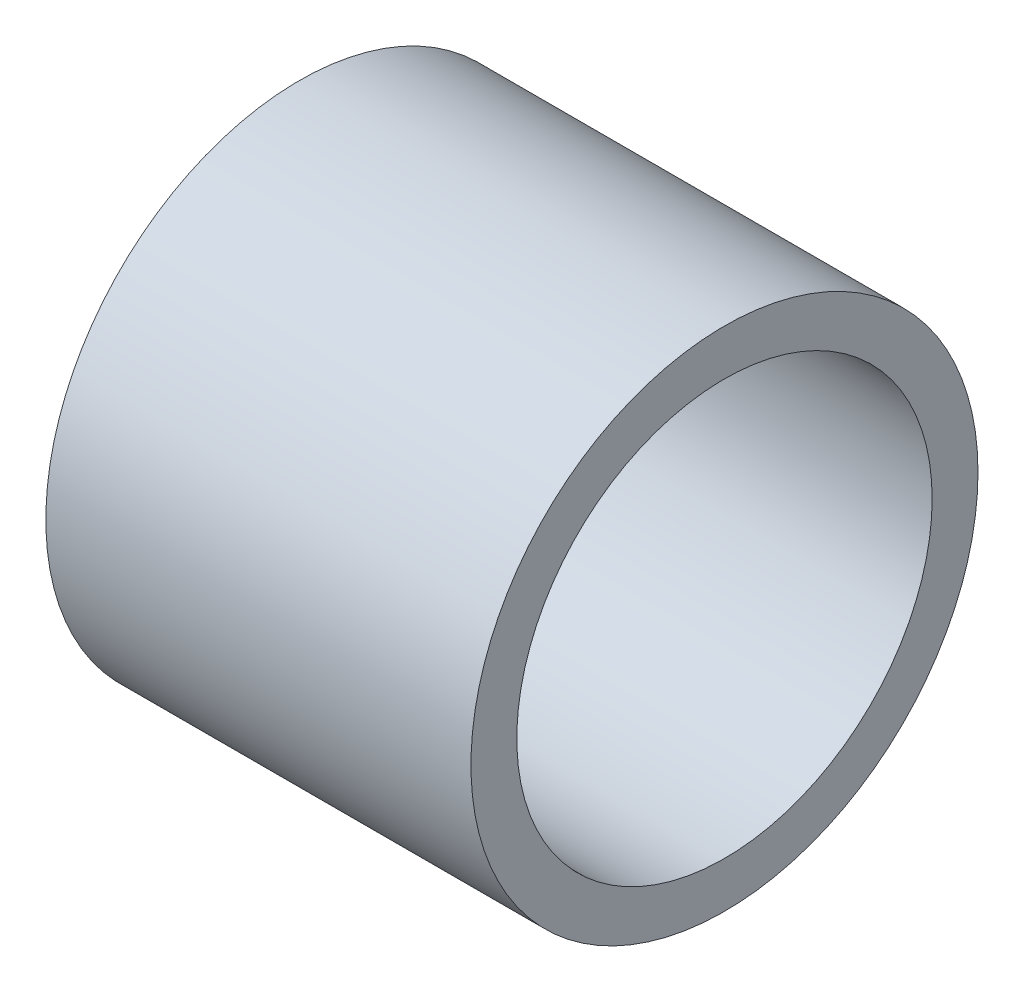
SolidWorks part; units mm, degrees
ref_plane "Front Plane" through (0, 0, 0) normal (0, 0, 1) x (1, 0, 0)
ref_plane "Top Plane" through (0, 0, 0) normal (0, 1, 0) x (1, 0, 0)
ref_plane "Right Plane" through (0, 0, 0) normal (1, 0, 0) x (0, 0, -1)
sketch "Sketch1" plane through (0, 0, 0) normal (1, 0, 0) x (0, 0, -1)
  circle A0 centre (0, 0) radius 1.6256
  circle A1 centre (0, 0) radius 1.9844
  dimension "D1" = 3.2512
  dimension "D2" = 3.9688
extrude "Boss-Extrude1" add sketch "Sketch1" along normal blind 3.3274
